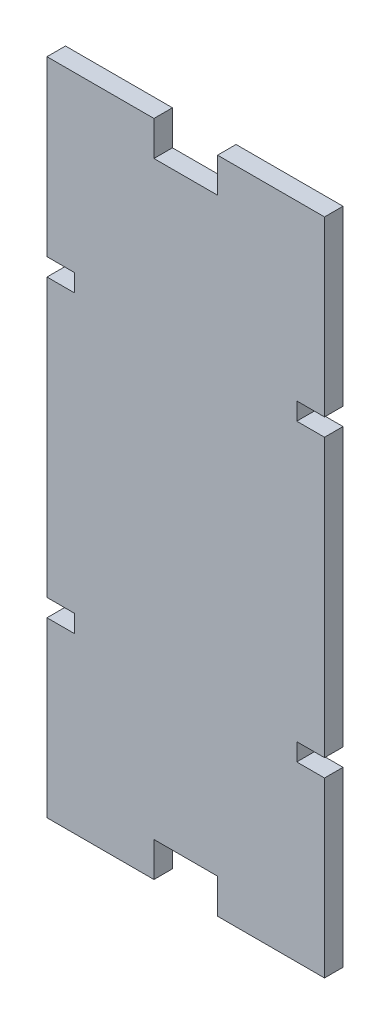
SolidWorks part; units mm, degrees
material "Pine"
ref_plane "Front Plane" through (0, 0, 0) normal (0, 0, 1) x (1, 0, 0)
ref_plane "Top Plane" through (0, 0, 0) normal (0, 1, 0) x (1, 0, 0)
ref_plane "Right Plane" through (0, 0, 0) normal (1, 0, 0) x (0, 0, -1)
sketch "Sketch1" plane through (0, 0, 0) normal (0, 0, 1) x (1, 0, 0)
  line L1 (-38.1, -90.4875) -> (38.1, -90.4875)
  line L2 (-38.1, -90.4875) -> (-38.1, 90.4875)
  line L3 (-38.1, 90.4875) -> (38.1, 90.4875)
  line L4 (38.1, -90.4875) -> (38.1, 90.4875)
  line L5 (-38.1, -90.4875) -> (38.1, 90.4875) construction
  line L6 (-38.1, 90.4875) -> (38.1, -90.4875) construction
  point P0 (0, 0)
  dimension "D1" = 180.975
  dimension "D2" = 76.2
extrude "Boss-Extrude1" add sketch "Sketch1" along normal blind 5.08
sketch "Sketch3" plane through (0, 0, 5.08) normal (0, 0, 1) x (1, 0, 0)
  line L6 (0, 0) -> (60.4565, 0) construction
  line L11 (0, 0) -> (0, 20.8202) construction
  line L20 (-8.7313, -90.4875) -> (-8.7313, -80.9625)
  line L21 (-38.1, -90.4875) -> (38.1, -90.4875) construction
  line L22 (-8.7313, -80.9625) -> (8.7312, -80.9625)
  line L23 (8.7312, -80.9625) -> (8.7313, -90.4875)
  line L24 (8.7313, -90.4875) -> (-8.7313, -90.4875)
  line L25 (8.7313, 90.4875) -> (-8.7313, 90.4875)
  line L26 (8.7312, 80.9625) -> (8.7313, 90.4875)
  line L27 (-8.7312, 80.9625) -> (8.7312, 80.9625)
  line L28 (-8.7313, 90.4875) -> (-8.7312, 80.9625)
  point P30 (0, -80.9625)
  dimension "D4" = 17.4625
  dimension "D5" = 9.525
extrude "Cut-Extrude1" cut sketch "Sketch3" against normal through all
sketch "Sketch4" plane through (0, 0, 5.08) normal (0, 0, 1) x (1, 0, 0)
  line L6 (-38.1, 42.926) -> (-30.48, 42.926)
  line L7 (-38.1, 90.4875) -> (-38.1, -90.4875) construction
  line L37 (-30.48, 42.926) -> (-30.48, 38.1)
  line L38 (-30.48, 38.1) -> (-38.1, 38.1)
  line L39 (-38.1, 38.1) -> (-38.1, 42.926)
  line L40 (0, 0) -> (0, 80.9625) construction
  line L41 (-8.7312, 80.9625) -> (8.7312, 80.9625) construction
  line L42 (0, 0) -> (38.1, 0) construction
  line L43 (38.1, -90.4875) -> (38.1, 90.4875) construction
  line L44 (38.1, 38.1) -> (38.1, 42.926)
  line L45 (30.48, 38.1) -> (38.1, 38.1)
  line L46 (30.48, 42.926) -> (30.48, 38.1)
  line L47 (38.1, 42.926) -> (30.48, 42.926)
  line L48 (38.1, -42.926) -> (30.48, -42.926)
  line L49 (30.48, -42.926) -> (30.48, -38.1)
  line L50 (30.48, -38.1) -> (38.1, -38.1)
  line L51 (38.1, -38.1) -> (38.1, -42.926)
  line L52 (-38.1, -38.1) -> (-38.1, -42.926)
  line L53 (-30.48, -38.1) -> (-38.1, -38.1)
  line L54 (-30.48, -42.926) -> (-30.48, -38.1)
  line L55 (-38.1, -42.926) -> (-30.48, -42.926)
  dimension "D1" = 4.826
  dimension "D2" = 7.62
  dimension "D3" = 38.1
extrude "Cut-Extrude2" cut sketch "Sketch4" against normal through all
